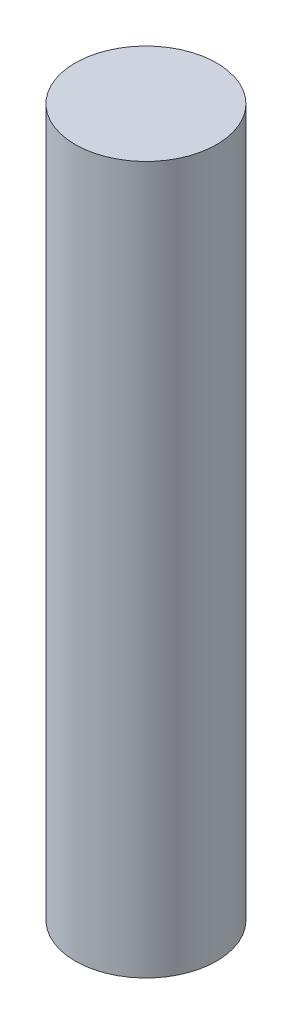
SolidWorks part; units mm, degrees
ref_plane "Front Plane" through (0, 0, 0) normal (0, 0, 1) x (1, 0, 0)
ref_plane "Top Plane" through (0, 0, 0) normal (0, 1, 0) x (1, 0, 0)
ref_plane "Right Plane" through (0, 0, 0) normal (1, 0, 0) x (0, 0, -1)
sketch "Sketch1" plane through (0, 0, 0) normal (0, 1, 0) x (1, 0, 0)
  circle A0 centre (0, 0) radius 4.5
  dimension "D1" = 9
extrude "Boss-Extrude1" add sketch "Sketch1" along normal blind 45
